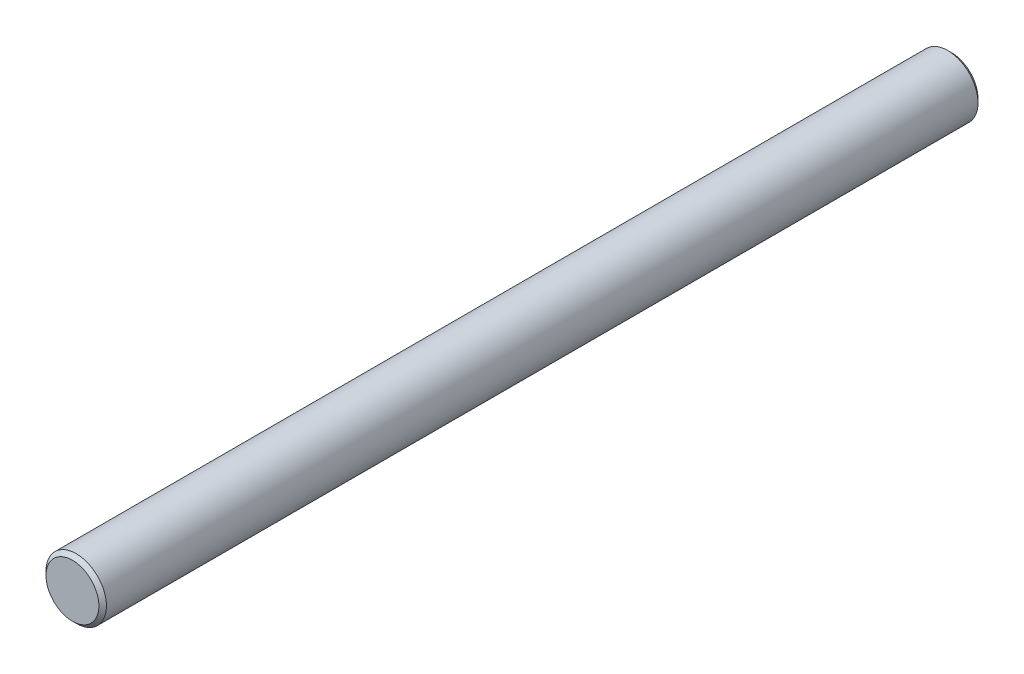
SolidWorks part; units mm, degrees
ref_plane "Front Plane" through (0, 0, 0) normal (0, 0, 1) x (1, 0, 0)
ref_plane "Top Plane" through (0, 0, 0) normal (0, 1, 0) x (1, 0, 0)
ref_plane "Right Plane" through (0, 0, 0) normal (1, 0, 0) x (0, 0, -1)
sketch "Sketch1" plane through (0, 0, 0) normal (0, 1, 0) x (1, 0, 0)
  line L0 (0, 0) -> (0, -121) construction
  line L1 (0, 0) -> (-4, 0) construction
  line L2 (-4, 0) -> (-4, -121) construction
  line L3 (-4, -121) -> (0, -121) construction
  line L4 (-1, 0) -> (-1, -121) construction
  line L5 (0, -2) -> (-4, -2) construction
  line L6 (-1, 0) -> (-4, 0)
  line L7 (0, -60.5) -> (-4, -60.5) construction
  line L8 (0, -2) -> (-1, -2)
  line L9 (-1, -2) -> (-1, 0)
  line L10 (0, -119) -> (-1, -119)
  line L11 (-1, -119) -> (-1, -121)
  line L12 (-4, 0) -> (-4, -121)
  line L13 (-4, -121) -> (-1, -121)
  line L14 (0, -119) -> (0, -2)
  dimension "D1" = 121
  dimension "D2" = 4
  dimension "D3" = 1
  dimension "D4" = 2
revolve "Revolve1" add sketch "Sketch1" angle 360 about L14
chamfer "Chamfer1" distance 0.5 angle 45 2 edges at (4, 0, 0) (4, 0, 121)
chamfer "Chamfer2" distance 0.3 angle 30 4 edges at (1, 0, 2) (1, 0, 0) (1, 0, 119) (1, 0, 121)
sketch "Sketch2" plane through (0, 28.2, 0) normal (0, 1, 0) x (1, 0, 0)
  line L1 (-9.057, -116.35) -> (14.1401, -116.35)
  line L2 (-9.057, -116.35) -> (-9.057, -128.1521)
  line L3 (-9.057, -128.1521) -> (14.1401, -128.1521)
  line L4 (14.1401, -116.35) -> (14.1401, -128.1521)
  line L5 (-18.75, -97.1) -> (18.75, -97.1) construction
  dimension "D1" = 19.25
extrude "Cut-Extrude1" cut sketch "Sketch2" against normal blind 50
chamfer "Chamfer3" distance 0.5 angle 45 1 edges at (-4, 0, 116.35)
